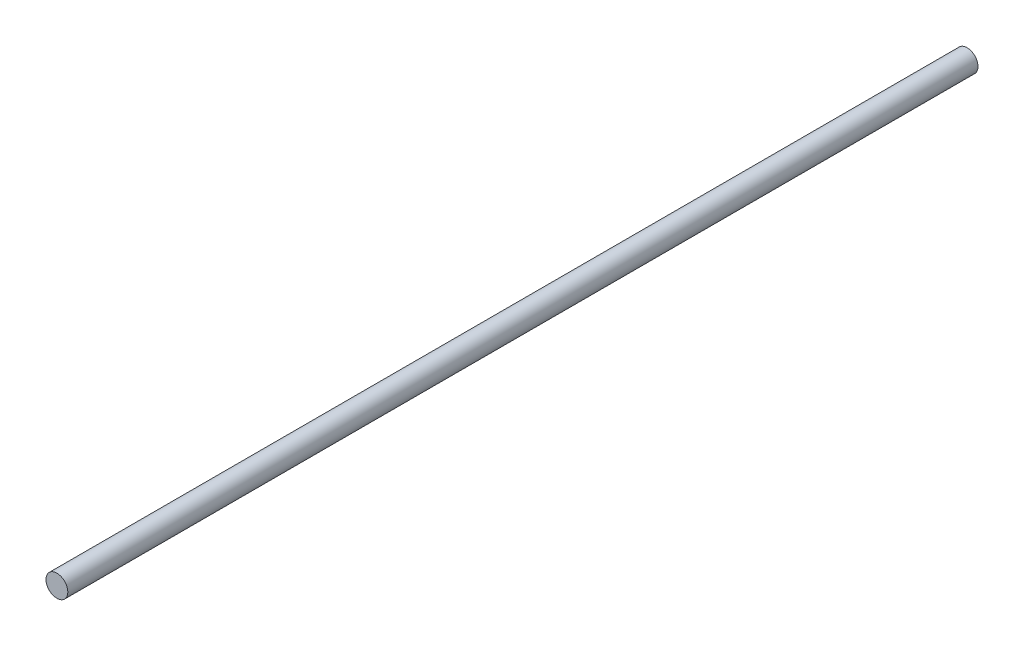
SolidWorks part; units mm, degrees
ref_plane "Front Plane" through (0, 0, 0) normal (0, 0, 1) x (1, 0, 0)
ref_plane "Top Plane" through (0, 0, 0) normal (0, 1, 0) x (1, 0, 0)
ref_plane "Right Plane" through (0, 0, 0) normal (1, 0, 0) x (0, 0, -1)
sketch "Sketch1" plane through (0, 0, 0) normal (0, 0, 1) x (1, 0, 0)
  circle A0 centre (0, 0) radius 3
  dimension "D1" = 6
extrude "Boss-Extrude1" add sketch "Sketch1" along normal blind 250.35
